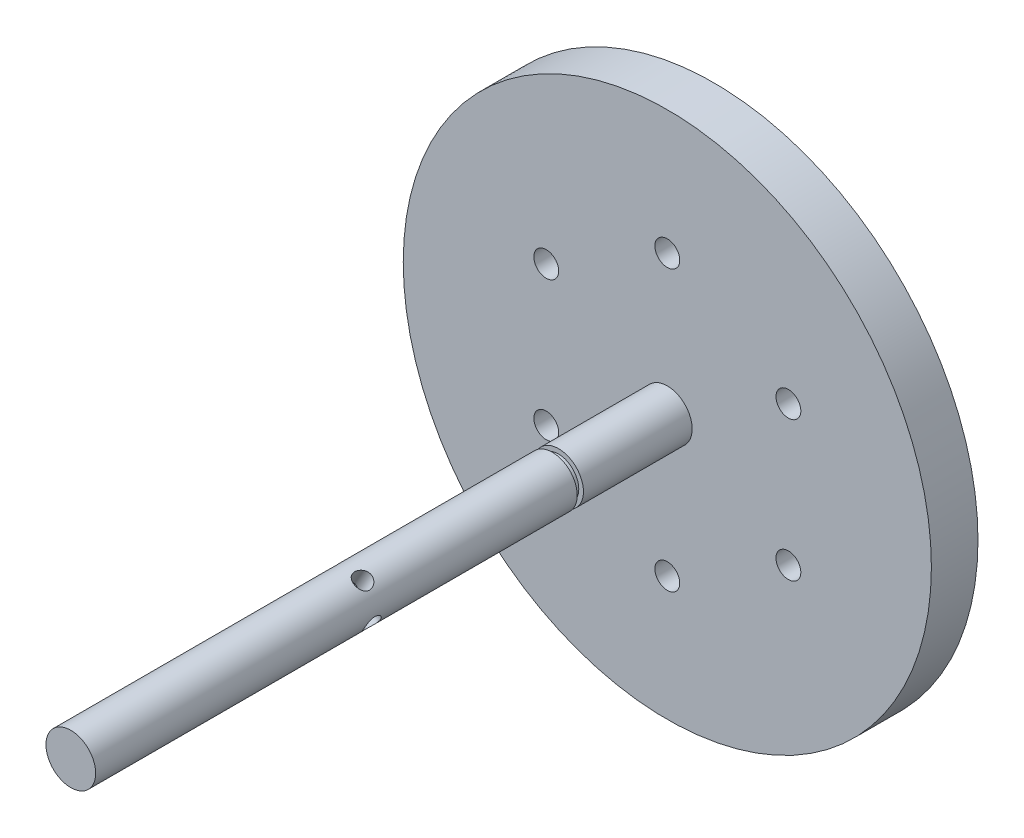
SolidWorks part; units mm, degrees
ref_plane "Front Plane" through (0, 0, 0) normal (0, 0, 1) x (1, 0, 0)
ref_plane "Top Plane" through (0, 0, 0) normal (0, 1, 0) x (1, 0, 0)
ref_plane "Right Plane" through (0, 0, 0) normal (1, 0, 0) x (0, 0, -1)
ref_plane "Plane1" through (0, 50, 0) normal (0, 1, 0) x (1, 0, 0)
sketch "Sketch1" plane through (0, 50, 0) normal (0, 1, 0) x (1, 0, 0)
  line L0 (85, -8) -> (0, -8)
  line L1 (0, -8) -> (0, -215)
  line L2 (0, -215) -> (8, -215)
  line L3 (8, -215) -> (8, -60)
  line L4 (8, -60) -> (6.5, -60)
  line L5 (6.5, -60) -> (6.5, -58)
  line L6 (6.5, -58) -> (8, -58)
  line L9 (8, -58) -> (8, -23)
  line L10 (8, -23) -> (85, -23)
  line L11 (85, -23) -> (85, -8)
  line L12 (0, -8) -> (0, -215) construction
  dimension "D1" = 85
  dimension "D2" = 8
  dimension "D3" = 1.5
  dimension "D4" = 2
  dimension "D5" = 35
  dimension "D6" = 155
  dimension "D9" = 15
revolve "Revolve1" add sketch "Sketch1" angle 360 about L12
hole_wizard "Ø8.0mm Dowel Hole1" positions "Sketch5" profile "Sketch4" hole size "Ø8.0" standard "ANSI Metric"
sketch "Sketch5" plane through (0, 0, 8) normal (0, 0, -1) x (-1, 0, 0)
  line L3 (0, 95) -> (0, 5) construction
  line L10 (38.9711, 72.5) -> (-38.9711, 27.5) construction
  line L12 (-38.9711, 72.5) -> (38.9711, 27.5) construction
  circle A0 centre (0, 50) radius 4.2284
  point P0 (0, 95)
  point P1 (-38.9711, 72.5)
  point P2 (-38.9711, 27.5)
  point P3 (0, 5)
  point P4 (38.9711, 27.5)
  point P5 (38.9711, 72.5)
  dimension "D1" = 90
  dimension "D2" = 45
  dimension "D3" = 45
  dimension "D4" = 45
sketch "Sketch4" plane through (0, 95, 8) normal (1, 0, 0) x (0, 1, 0)
  line L0 (0, 0) -> (0, 32.4034)
  line L1 (0, 32.4034) -> (4, 30)
  line L2 (4, 30) -> (4, 0)
  line L5 (4, 0) -> (0, 0)
  line L10 (0, 32.4034) -> (-4, 30) construction
  line L11 (0, -6.35) -> (0, 107.95) construction
  dimension "Hole Dia." = 8
  dimension "Hole Depth" = 30
  dimension "Drill Angle" = 118
sketch "Sketch7" plane through (0, 0, 0) normal (0, 0, 1) x (1, 0, 0)
  line L0 (0, 0) -> (184.3674, 0) construction
  line L1 (184.3674, 0) -> (0, -319.3337) construction
  line L2 (0, -319.3337) -> (0, 0) construction
  line L3 (184.3674, 0) -> (0, 106.4446) construction
  line L4 (0, 0) -> (0, 106.4446) construction
  dimension "D1" = 60
  dimension "D2" = 30
sketch "Sketch8" plane through (0, 0, 0) normal (0, 1, 0) x (1, 0, 0)
  line L0 (184.3674, 0) -> (184.3674, -122.1969) construction
  line L1 (184.3674, 0) -> (0, 0) construction
  line L2 (184.3674, -122.1969) -> (0, -122.1969) construction
  line L3 (0, -122.1969) -> (0, 0) construction
sketch "Sketch9" plane through (0, 0, 0) normal (1, 0, 0) x (0, 0, -1)
  line L0 (-122.1969, 0) -> (-122.1969, -319.3337) construction
  line L1 (-122.1969, -319.3337) -> (0, -319.3337) construction
  line L2 (-122.1969, 0) -> (0, 0) construction
  line L3 (0, -319.3337) -> (0, 0) construction
ref_plane "Plane2" through (138.2755, -79.8334, 0) normal (0.866, -0.5, 0) x (-0.5, -0.866, 0)
sketch "Sketch10" plane through (138.2755, -79.8334, 0) normal (0.866, -0.5, 0) x (-0.5, -0.866, 0)
  circle A0 centre (-43.3013, -125) radius 2.75
extrude "Cut-Extrude1" cut sketch "Sketch10" against normal blind 260
ref_plane "Plane3" through (46.0918, 79.8334, 0) normal (0.5, 0.866, 0) x (0.866, -0.5, 0)
sketch "Sketch11" plane through (46.0918, 79.8334, 0) normal (0.5, 0.866, 0) x (0.866, -0.5, 0)
  circle A0 centre (-25, -125) radius 2.75
extrude "Cut-Extrude2" cut sketch "Sketch11" against normal blind 260
sketch "Sketch12" plane through (0, 0, 8) normal (0, 0, -1) x (-1, 0, 0)
  line L0 (-38.9711, 72.5) -> (38.9711, 27.5) construction
  line L1 (-38.9711, 27.5) -> (38.9711, 72.5) construction
  circle A0 centre (0, 50) radius 4
extrude "Cut-Extrude3" cut sketch "Sketch12" against normal blind 30
